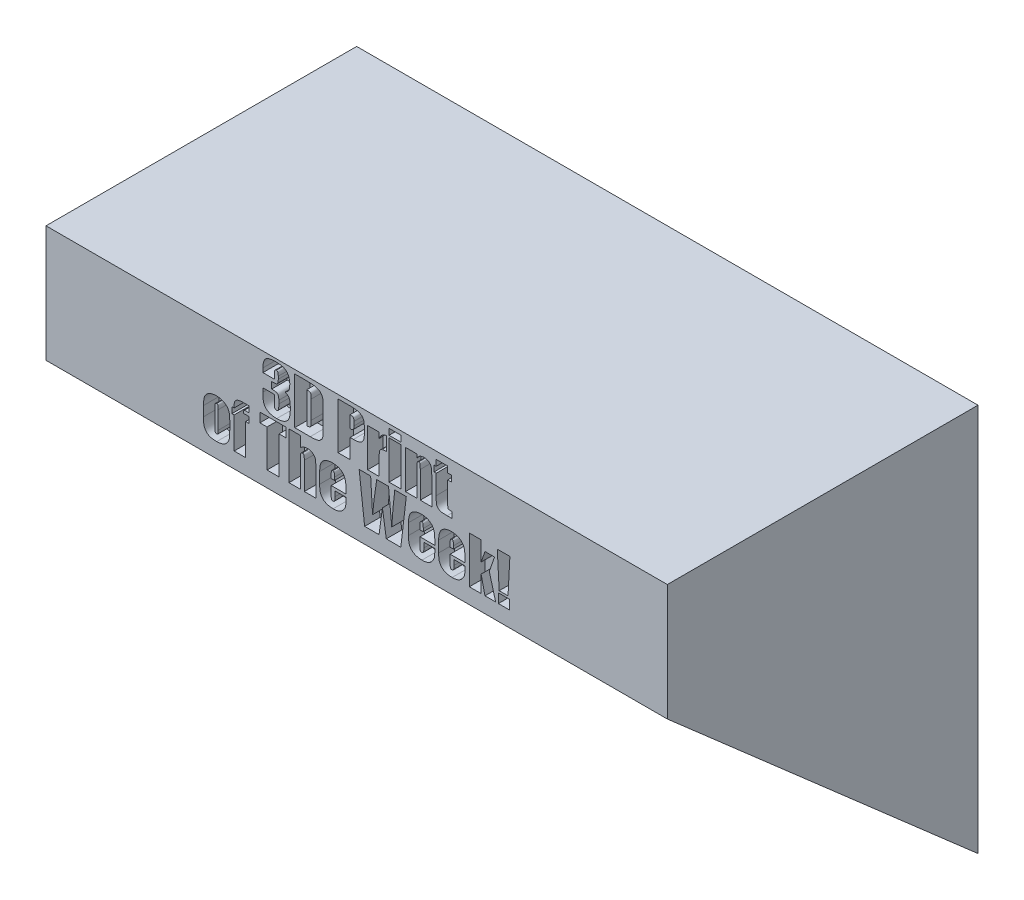
SolidWorks part; units mm, degrees
ref_plane "Front Plane" through (0, 0, 0) normal (0, 0, 1) x (1, 0, 0)
ref_plane "Top Plane" through (0, 0, 0) normal (0, 1, 0) x (1, 0, 0)
ref_plane "Right Plane" through (0, 0, 0) normal (1, 0, 0) x (0, 0, -1)
sketch "Sketch1" plane through (0, 0, 0) normal (1, 0, 0) x (0, 0, -1)
  line L0 (0, 0) -> (0, 127)
  line L1 (0, 127) -> (-101.6, 127)
  line L2 (-101.6, 127) -> (-101.6, 88.9)
  line L3 (-101.6, 88.9) -> (0, 0)
  dimension "D1" = 101.6
  dimension "D2" = 38.1
  dimension "D3" = 127
extrude "Boss-Extrude1" add sketch "Sketch1" along normal mid plane 203.2
sketch "Sketch2" plane through (0, 0, 0) normal (0, 0, 1) x (1, 0, 0)
  line L0 (101.6, 0) -> (-101.6, 0) construction
  line L1 (101.6, 88.9) -> (101.6, 0) construction
  line L2 (-88.9, 0) -> (88.9, 0)
  arc A0 (-88.9, 0) -> (88.9, 0) centre (0, -49.1869) cw
  dimension "D1" = 101.6
  dimension "D2" = 12.7
  dimension "D3" = 12.7
extrude "Cut-Extrude1" cut sketch "Sketch2" along normal through all
sketch "Sketch3" plane through (0, 0, 101.6) normal (0, 0, 1) x (1, 0, 0)
  line L0 (50.8, 110.49) -> (-50.8, 110.49) construction
  line L1 (50.8, 93.98) -> (-50.8, 93.98) construction
  line L2 (101.6, 127) -> (-101.6, 127) construction
  text T0 "3D Print" font "Impact" height 15.24
  text T1 "of The Week!" font "Impact" height 15.24
  point P3 (0, 110.49)
  point P6 (0, 93.98)
  dimension "D1" = 101.6
  dimension "D2" = 16.51
  dimension "D3" = 16.51
extrude "Cut-Extrude2" cut sketch "Sketch3" against normal blind 5.08
